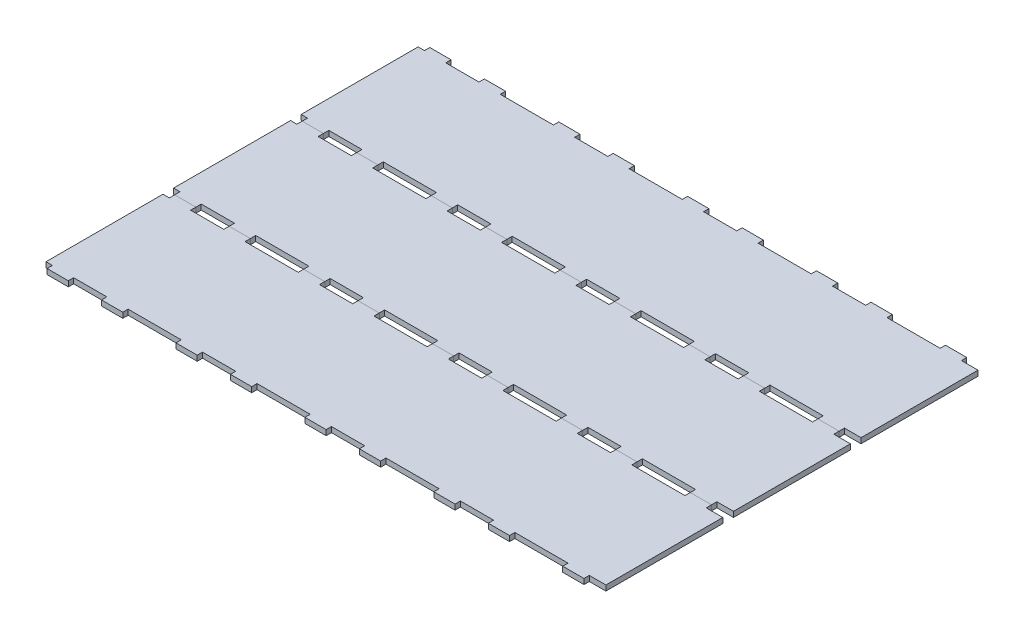
SolidWorks part; units mm, degrees
material "Cedar"
ref_plane "Front Plane" through (0, 0, 0) normal (0, 0, 1) x (1, 0, 0)
ref_plane "Top Plane" through (0, 0, 0) normal (0, 1, 0) x (1, 0, 0)
ref_plane "Right Plane" through (0, 0, 0) normal (1, 0, 0) x (0, 0, -1)
sketch "Sketch1" plane through (0, 0, 0) normal (0, 1, 0) x (1, 0, 0)
  line L1 (-360.8183, 76.2) -> (360.8183, 76.2)
  line L2 (-360.8183, 76.2) -> (-360.8183, -76.2)
  line L3 (-360.8183, -76.2) -> (360.8183, -76.2)
  line L4 (360.8183, 76.2) -> (360.8183, -76.2)
  line L5 (-360.8183, 76.2) -> (360.8183, -76.2) construction
  line L6 (-360.8183, -76.2) -> (360.8183, 76.2) construction
  point P0 (0, 0)
  dimension "D1" = 721.6366
  dimension "D2" = 152.4
extrude "Boss-Extrude1" add sketch "Sketch1" along normal blind 6.35
sketch "Sketch2" plane through (0, 6.35, 0) normal (0, 1, 0) x (1, 0, 0)
  line L0 (0, -76.2) -> (0, -69.85) construction
  line L1 (-32.5397, -69.85) -> (32.5397, -69.85) construction
  line L2 (-45.2397, -69.85) -> (-19.8397, -69.85) construction
  line L3 (-45.2397, -69.85) -> (-45.2397, -76.2) construction
  line L4 (-45.2397, -76.2) -> (-19.8397, -76.2) construction
  line L5 (-19.8397, -69.85) -> (-19.8397, -76.2)
  line L6 (-45.2397, -69.85) -> (-19.8397, -76.2) construction
  line L7 (-45.2397, -76.2) -> (-19.8397, -69.85) construction
  line L8 (-360.8183, -76.2) -> (360.8183, -76.2) construction
  line L9 (-19.8397, -69.85) -> (19.8397, -69.85)
  line L10 (19.8397, -69.85) -> (45.2397, -69.85) construction
  line L11 (19.8397, -69.85) -> (19.8397, -76.2)
  line L12 (19.8397, -76.2) -> (45.2397, -76.2) construction
  line L13 (45.2397, -69.85) -> (45.2397, -76.2) construction
  line L14 (19.8397, -69.85) -> (45.2397, -76.2) construction
  line L15 (19.8397, -76.2) -> (45.2397, -69.85) construction
  line L16 (19.8397, -76.2) -> (-19.8397, -76.2)
  line L17 (-45.2397, -76.2) -> (-45.2397, -69.85)
  line L18 (-45.2397, -69.85) -> (-76.9897, -69.85)
  line L19 (-76.9897, -69.85) -> (-76.9897, -76.2)
  line L20 (-76.9897, -76.2) -> (-45.2397, -76.2)
  line L21 (45.2397, -69.85) -> (76.9897, -69.85)
  line L22 (76.9897, -69.85) -> (76.9897, -76.2)
  line L23 (76.9897, -76.2) -> (45.2397, -76.2)
  line L24 (45.2397, -76.2) -> (45.2397, -69.85)
  point P5 (0, -69.85)
  point P6 (-32.5397, -73.025)
  point P11 (-32.5397, -69.85)
  point P17 (32.5397, -73.025)
  point P24 (32.5397, -69.85)
  dimension "D1" = 39.6793
  dimension "D2" = 25.4
  dimension "D3" = 6.35
  dimension "D4" = 76.9897
  dimension "D5" = 25.4
  dimension "D6" = 6.35
  dimension "D7" = 76.9897
extrude "Cut-Extrude1" cut sketch "Sketch2" against normal through all
pattern_linear "LPattern1" count 3 spacing 153.9793 along (1, 0, 0) count 3 spacing 153.9793 along (-1, 0, 0) of "Cut-Extrude1"
mirror "Mirror1" about plane through (0, 0, 0) normal (0, 0, 1) of "LPattern1", "Cut-Extrude1"
sketch "Sketch3" plane through (0, 6.35, 0) normal (0, 1, 0) x (1, 0, 0)
  line L0 (307.9586, 69.85) -> (307.9586, -76.2)
  line L1 (327.7983, 69.85) -> (288.119, 69.85) construction
  line L2 (307.9586, -76.2) -> (360.8183, -76.2)
  line L3 (360.8183, -76.2) -> (360.8183, 76.2)
  line L4 (360.8183, 76.2) -> (307.9586, 76.2)
  line L5 (307.9586, 76.2) -> (307.9586, 69.85)
extrude "Cut-Extrude2" cut sketch "Sketch3" against normal through all
pattern_linear "LPattern2" count 3 spacing 152.4 along (0, 0, 1) of bodies 105
